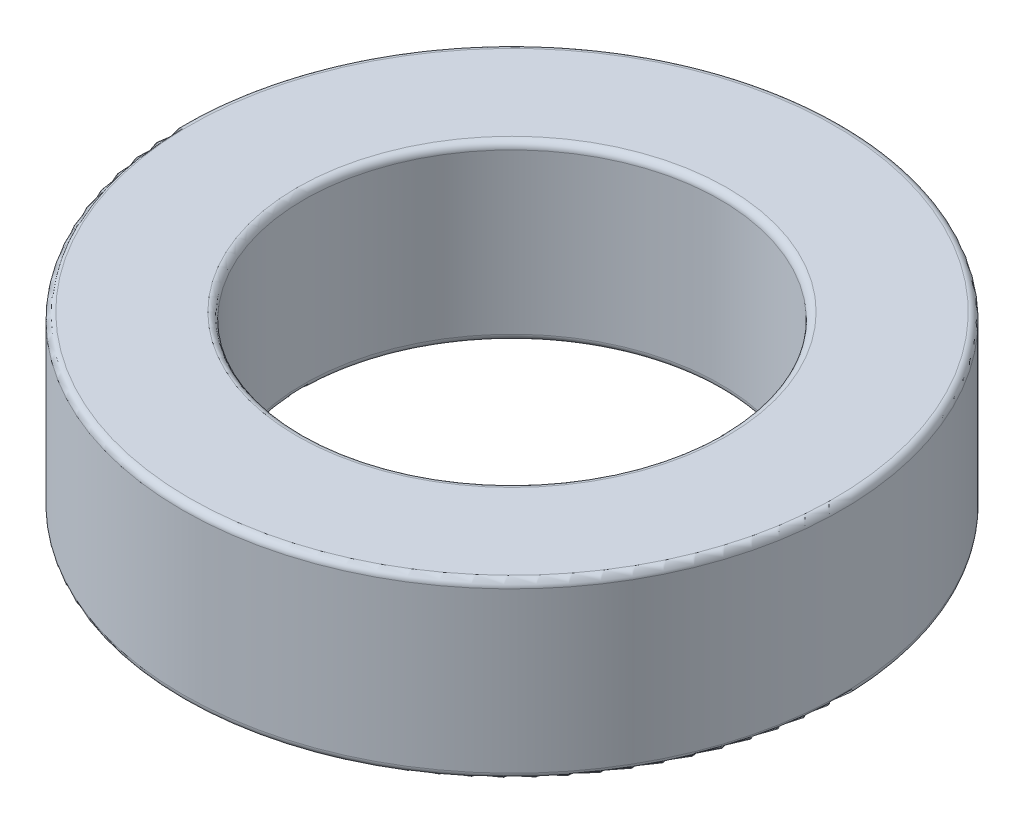
SolidWorks part; units mm, degrees
ref_plane "Front Plane" through (0, 0, 0) normal (0, 0, 1) x (1, 0, 0)
ref_plane "Top Plane" through (0, 0, 0) normal (0, 1, 0) x (1, 0, 0)
ref_plane "Right Plane" through (0, 0, 0) normal (1, 0, 0) x (0, 0, -1)
sketch "Sketch1" plane through (0, 0, 0) normal (0, 1, 0) x (1, 0, 0)
  circle A0 centre (0, 0) radius 9.5
  circle A1 centre (0, 0) radius 6
  dimension "D1" = 19
  dimension "D2" = 12
extrude "Boss-Extrude1" add sketch "Sketch1" along normal blind 5
fillet "Fillet1" radius 0.2 4 edges at (0, 0, 6) (0, 5, 6) (0, 0, 9.5) (0, 5, 9.5)
